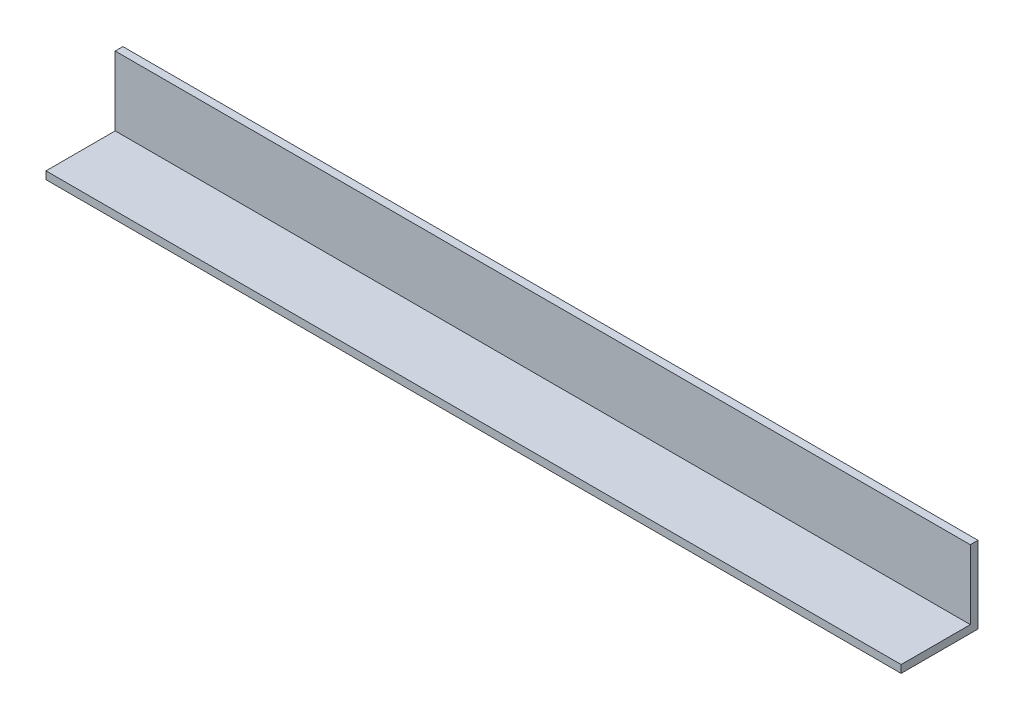
SolidWorks part; units mm, degrees
ref_plane "Front Plane" through (0, 0, 0) normal (0, 0, 1) x (1, 0, 0)
ref_plane "Top Plane" through (0, 0, 0) normal (0, 1, 0) x (1, 0, 0)
ref_plane "Right Plane" through (0, 0, 0) normal (1, 0, 0) x (0, 0, -1)
sketch "Sketch1" plane through (0, 0, 0) normal (0, 1, 0) x (1, 0, 0)
  line L1 (-222.5, 20) -> (222.5, 20)
  line L2 (-222.5, 20) -> (-222.5, -20)
  line L3 (-222.5, -20) -> (222.5, -20)
  line L4 (222.5, 20) -> (222.5, -20)
  line L5 (-222.5, 20) -> (222.5, -20) construction
  line L6 (-222.5, -20) -> (222.5, 20) construction
  point P0 (0, 0)
  dimension "D1" = 40
  dimension "D2" = 445
extrude "Boss-Extrude1" add sketch "Sketch1" along normal blind 4
sketch "Sketch2" plane through (0, 4, 0) normal (0, 1, 0) x (1, 0, 0)
  line L1 (-222.5, 20) -> (222.5, 20)
  line L2 (222.5, 16) -> (-222.5, 16)
  line L3 (222.5, 16) -> (-222.5, 16)
  line L4 (222.5, 20) -> (222.5, 16)
  line L5 (-222.5, 20) -> (-222.5, 16)
  dimension "D1" = 4
extrude "Boss-Extrude2" add sketch "Sketch2" along normal blind 36
